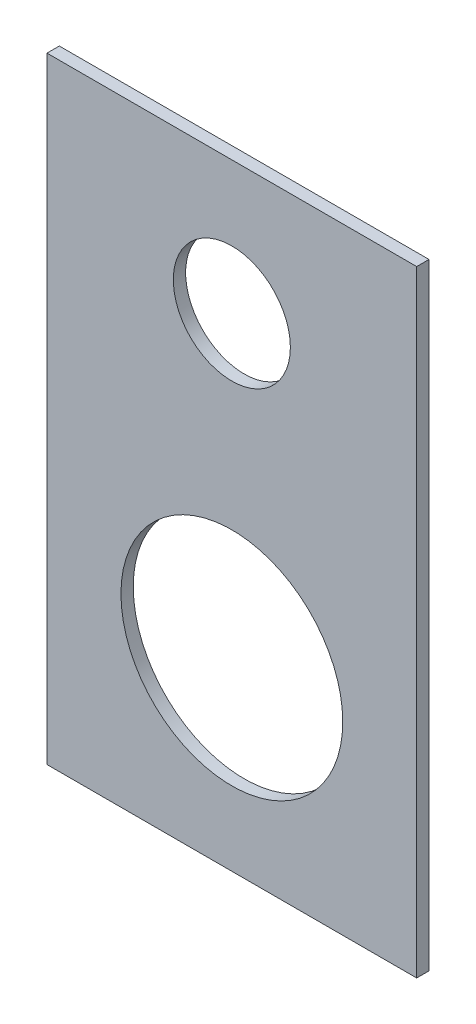
SolidWorks part; units mm, degrees
ref_plane "Front Plane" through (0, 0, 0) normal (0, 0, 1) x (1, 0, 0)
ref_plane "Top Plane" through (0, 0, 0) normal (0, 1, 0) x (1, 0, 0)
ref_plane "Right Plane" through (0, 0, 0) normal (1, 0, 0) x (0, 0, -1)
sketch "Sketch1" plane through (0, 0, 0) normal (0, 0, 1) x (1, 0, 0)
  line L0 (0, 150) -> (300, 150) construction
  line L1 (0, 0) -> (300, 0)
  line L2 (0, 0) -> (0, 500)
  line L3 (0, 500) -> (300, 500)
  line L4 (300, 0) -> (300, 500)
  line L5 (150, 0) -> (150, 500) construction
  line L6 (150, 150) -> (300, 150) construction
  line L7 (150, 280) -> (300, 280) construction
  circle A0 centre (150, 150) radius 90
  circle A1 centre (150, 392) radius 47.5
  dimension "D3" = 180
  dimension "D4" = 150
  dimension "D5" = 280
  dimension "D8" = 95
  dimension "D1" = 300
  dimension "D2" = 500
  dimension "D6" = 108
extrude "Extrude1" add sketch "Sketch1" against normal blind 10
